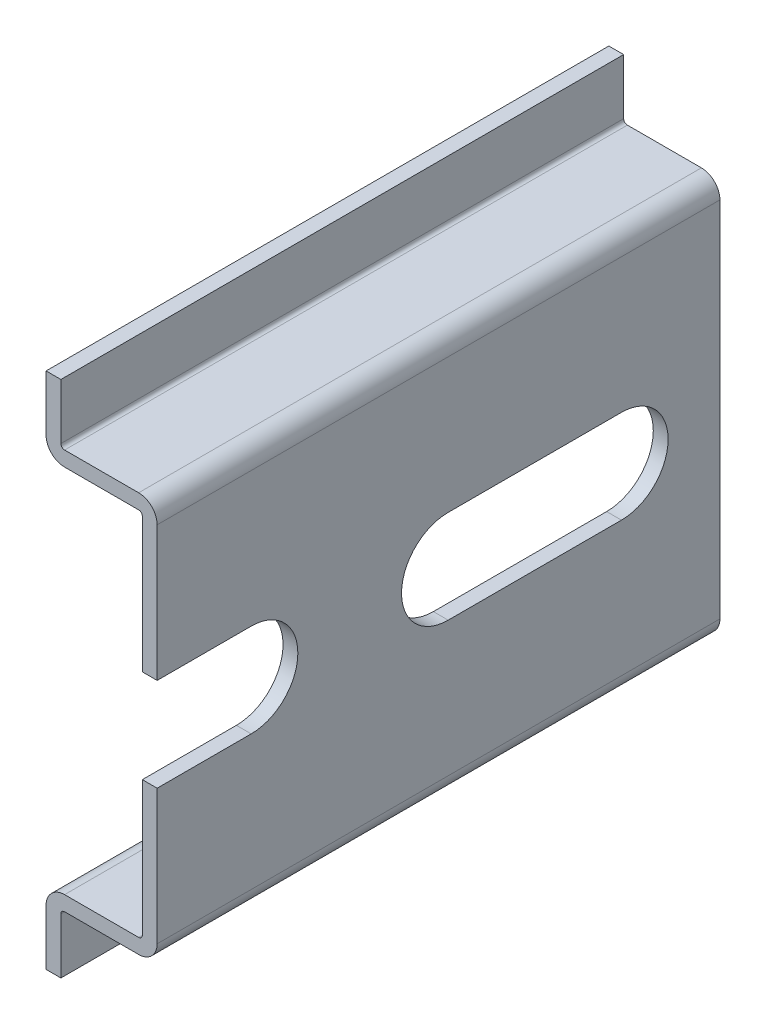
SolidWorks part; units mm, degrees
material "Plain Carbon Steel"
ref_plane "Front Plane" through (0, 0, 0) normal (0, 0, 1) x (1, 0, 0)
ref_plane "Top Plane" through (0, 0, 0) normal (0, 1, 0) x (1, 0, 0)
ref_plane "Right Plane" through (0, 0, 0) normal (1, 0, 0) x (0, 0, -1)
sketch "Sketch1" plane through (0, 0, 0) normal (0, 0, 1) x (1, 0, 0)
  line L0 (0, -13.5) -> (0, 13.5) construction
  line L1 (0, 13.5) -> (-6.5, 13.5) construction
  line L2 (-6.5, 13.5) -> (-6.5, 17.5) construction
  line L3 (0, -13.5) -> (-6.5, -13.5) construction
  line L4 (-6.5, -13.5) -> (-6.5, -17.5) construction
  line L5 (-7.5, 0) -> (0, 0) construction
  line L6 (-6.5, 17.5) -> (-7.5, 17.5) construction
  line L7 (-7.5, 0) -> (-7.5, 17.5) construction
  dimension "D1" = 27
  dimension "Height" = 35
  dimension "Depth" = 7.5
  dimension "Metal Thickness" = 1
sketch "Sketch2" plane through (0, 0, 0) normal (1, 0, 0) x (0, 0, -1)
  line L0 (0, 0) -> (-50.8, 0) construction
  line L1 (-6.35, 17.5) -> (-6.35, -17.5) construction
  line L2 (-44.45, 17.5) -> (-44.45, -17.5) construction
  line L3 (-6.35, 17.5) -> (-44.45, 17.5) construction
  line L4 (-25.4, 0) -> (-25.4, 17.5) construction
  point P8 (-44.45, 0)
  point P9 (-6.35, 0)
  dimension "Length" = 50.8
  dimension "D1" = 38.1
sketch "Sketch3" plane through (0, 0, 0) normal (0, 0, 1) x (1, 0, 0)
  line L0 (-6.5, -13.5) -> (-6.5, -17.5) construction
  line L1 (0, -13.5) -> (-6.5, -13.5) construction
  line L2 (0, -13.5) -> (0, 13.5) construction
  line L3 (0, 13.5) -> (-6.5, 13.5) construction
  line L4 (-6.5, 13.5) -> (-6.5, 17.5) construction
  line L5 (-6.5, -13.5) -> (-6.5, -17.5)
  line L6 (0, -13.5) -> (-6.5, -13.5)
  line L7 (0, -13.5) -> (0, 13.5)
  line L8 (0, 13.5) -> (-6.5, 13.5)
  line L9 (-6.5, 13.5) -> (-6.5, 17.5)
extrude "Extrude-Thin1" add sketch "Sketch3" along normal up to vertex (50.8 mm away) thin
sketch "Sketch4" plane through (0, 0, 0) normal (1, 0, 0) x (0, 0, -1)
  line L0 (0, 0) -> (-62.1077, 0) construction
  line L1 (-6.65, 0) -> (-18.35, 0) construction
  line L2 (-6.65, -3.15) -> (-18.35, -3.15)
  line L3 (-6.65, 3.15) -> (-18.35, 3.15)
  arc A0 (-6.65, -3.15) -> (-6.65, 3.15) centre (-6.65, 0) ccw
  arc A1 (-18.35, 3.15) -> (-18.35, -3.15) centre (-18.35, 0) ccw
  point P5 (-12.5, 0)
  point P10 (-3.5, 0)
  point P11 (-21.5, 0)
  point P12 (-37.5, 0)
  dimension "D1" = 18
  dimension "Mounting Hole Diameter" = 6.3
  dimension "D3" = 12.5
  dimension "Mounting Hole C to C" = 25
extrude "Cut-Extrude1" cut sketch "Sketch4" against normal through all both and the other way through all
pattern_linear "LPattern1" count 2 spacing 25 along (0, 0, 1) of "Cut-Extrude1"
fillet "Fillet1" radius 0.25 4 edges at (-6.5, 13.5, 25.4) (-6.5, -13.5, 25.4) (-1, 12.5, 25.4) (-1, -12.5, 25.4)
fillet "Fillet2" radius 1.25 4 edges at (-7.5, -12.5, 25.4) (0, -13.5, 25.4) (0, 13.5, 25.4) (-7.5, 12.5, 25.4)
ref_plane "Contact Plane 1" through (-1, 0, 0) normal (-1, 0, 0) x (0, 0, 1)
sketch "Sketch5" plane through (-7.5, 0, 0) normal (-1, 0, 0) x (0, 0, 1)
  line L0 (0, -17.5) -> (0, -13.75) construction
  line L5 (50.8, 17.5) -> (38, 17.5)
  line L6 (50.8, 17.5) -> (50.8, -17.5)
  line L7 (50.8, -17.5) -> (38, -17.5)
  line L8 (38, 17.5) -> (38, -17.5)
  point P8 (0, -17.5)
  point P10 (0, 17.5)
  point P12 (50.8, 17.5)
  point P14 (50.8, -17.5)
  dimension "D1" = 38
extrude "Cut-Extrude2" cut sketch "Sketch5" against normal through all
equation "\"D3@LPattern1\" = \"Mounting Hole C to C@Sketch4\""
equation "\"D1@LPattern1\"=\"Length@Sketch2\" / \"D3@LPattern1\""
equation "\"D5@Extrude-Thin1\"=\"Metal Thickness@Sketch1\""
equation "\"D3@Sketch4\"=\"Mounting Hole C to C@Sketch4\"/2"
equation "\"D1@Sketch2\"=\"Length@Sketch2\"*.75"
